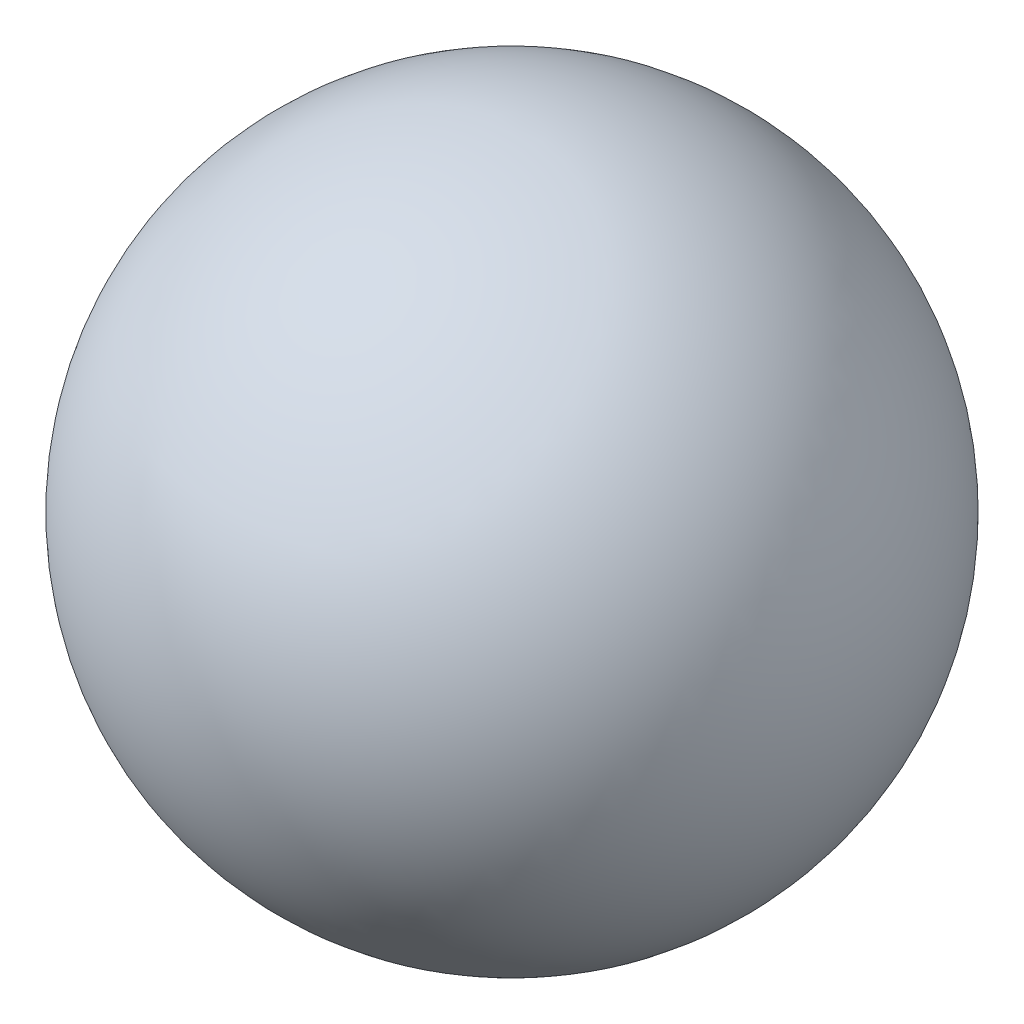
SolidWorks part; units mm, degrees
ref_plane "Front Plane" through (0, 0, 0) normal (0, 0, 1) x (1, 0, 0)
ref_plane "Top Plane" through (0, 0, 0) normal (0, 1, 0) x (1, 0, 0)
ref_plane "Right Plane" through (0, 0, 0) normal (1, 0, 0) x (0, 0, -1)
sketch "Sketch1" plane through (0, 0, 0) normal (1, 0, 0) x (0, 0, -1)
  line L0 (0, 10) -> (0, -10.1042) construction
  line L1 (0, 10) -> (0, -10)
  arc A0 (0, 10) -> (0, -10) centre (0, 0) ccw
  dimension "D1" = 10
revolve "Revolve3" add sketch "Sketch1" angle 360 about L0
